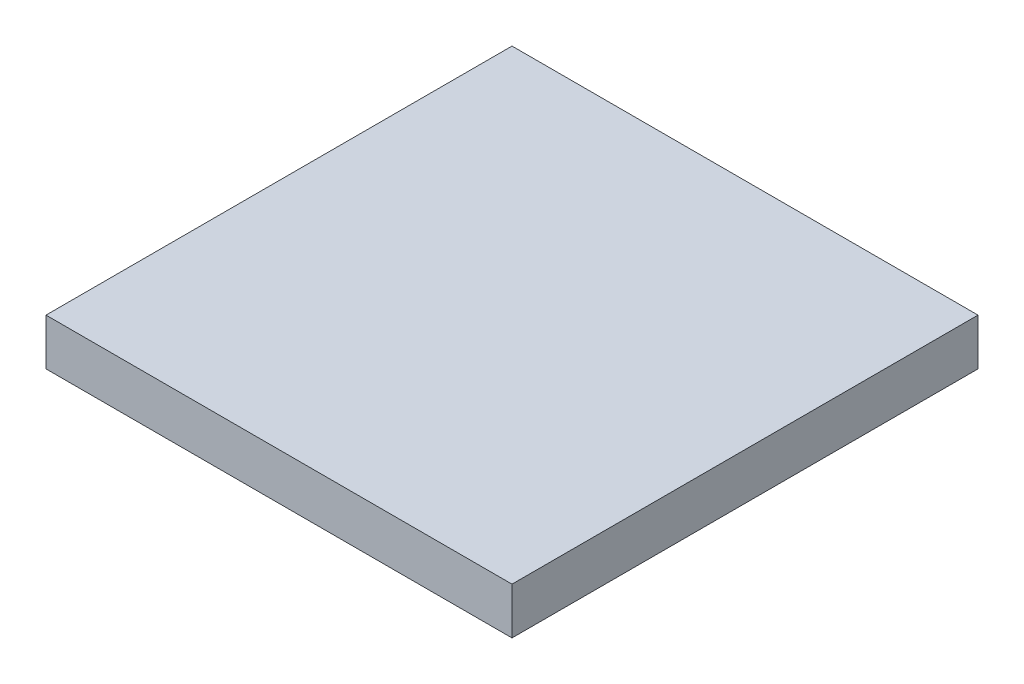
SolidWorks part; units mm, degrees
ref_plane "Front Plane" through (0, 0, 0) normal (0, 0, 1) x (1, 0, 0)
ref_plane "Top Plane" through (0, 0, 0) normal (0, 1, 0) x (1, 0, 0)
ref_plane "Right Plane" through (0, 0, 0) normal (1, 0, 0) x (0, 0, -1)
sketch "Sketch1" plane through (0, 0, 0) normal (0, 0, 1) x (1, 0, 0)
  line L1 (-500, -50) -> (500, -50)
  line L2 (-500, -50) -> (-500, 50)
  line L3 (-500, 50) -> (500, 50)
  line L4 (500, -50) -> (500, 50)
  line L5 (-500, -50) -> (500, 50) construction
  line L6 (-500, 50) -> (500, -50) construction
  point P0 (0, 0)
  dimension "D1" = 100
  dimension "D2" = 1000
extrude "Boss-Extrude1" add sketch "Sketch1" along normal blind 1000
